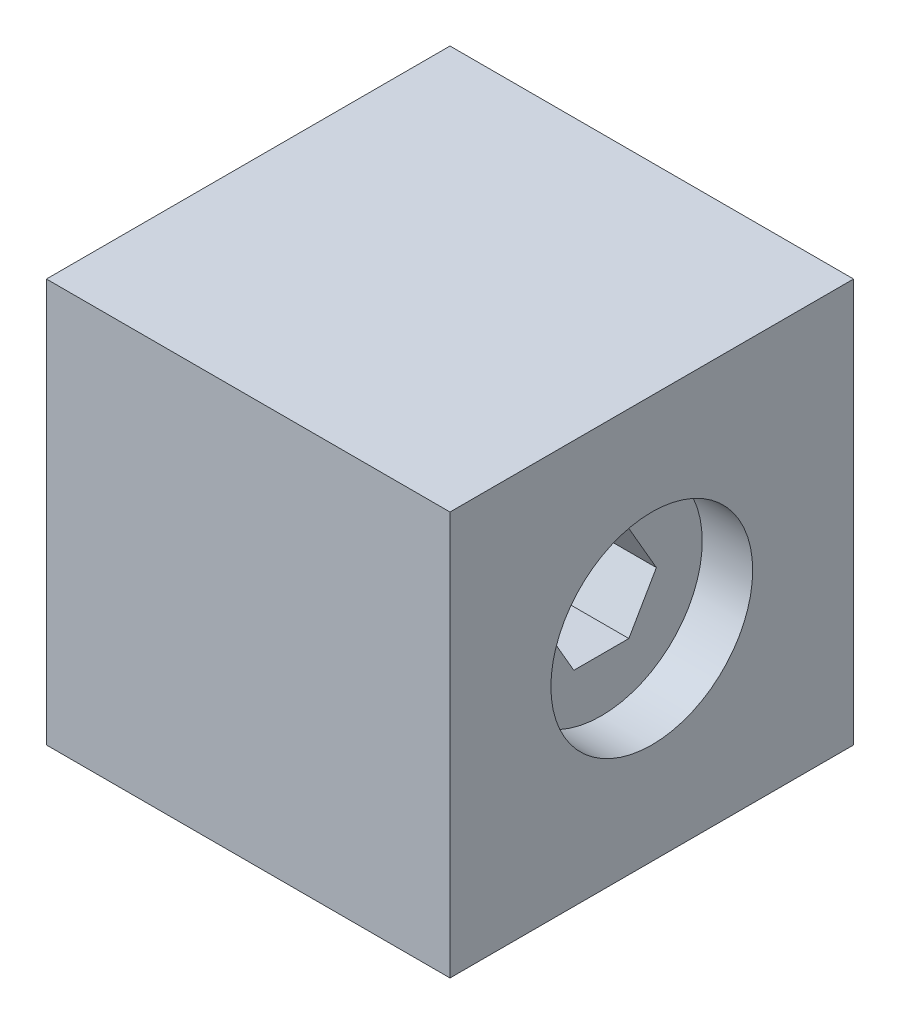
SolidWorks part; units mm, degrees
ref_plane "Front Plane" through (0, 0, 0) normal (0, 0, 1) x (1, 0, 0)
ref_plane "Top Plane" through (0, 0, 0) normal (0, 1, 0) x (1, 0, 0)
ref_plane "Right Plane" through (0, 0, 0) normal (1, 0, 0) x (0, 0, -1)
sketch "Sketch2" plane through (0, 0, 0) normal (0, 1, 0) x (1, 0, 0)
  line L1 (-25.4, -25.4) -> (25.4, -25.4)
  line L2 (-25.4, -25.4) -> (-25.4, 25.4)
  line L3 (-25.4, 25.4) -> (25.4, 25.4)
  line L4 (25.4, -25.4) -> (25.4, 25.4)
  line L5 (-25.4, -25.4) -> (25.4, 25.4) construction
  line L6 (-25.4, 25.4) -> (25.4, -25.4) construction
  point P0 (0, 0)
  dimension "D1" = 50.8
  dimension "D2" = 50.8
extrude "Boss-Extrude1" add sketch "Sketch2" along normal blind 50.8
sketch "Sketch3" plane through (0, 0, 0) normal (0, -1, 0) x (1, 0, 0)
  line L1 (-11.176, 11.176) -> (11.176, 11.176)
  line L2 (-11.176, 11.176) -> (-11.176, -11.176)
  line L3 (-11.176, -11.176) -> (11.176, -11.176)
  line L4 (11.176, 11.176) -> (11.176, -11.176)
  line L5 (-11.176, 11.176) -> (11.176, -11.176) construction
  line L6 (-11.176, -11.176) -> (11.176, 11.176) construction
  line L7 (-12.7, 12.7) -> (12.7, 12.7)
  line L8 (-12.7, 12.7) -> (-12.7, -12.7)
  line L9 (-12.7, -12.7) -> (12.7, -12.7)
  line L10 (12.7, 12.7) -> (12.7, -12.7)
  line L11 (-12.7, 12.7) -> (12.7, -12.7) construction
  line L12 (-12.7, -12.7) -> (12.7, 12.7) construction
  point P0 (0, 0)
  point P6 (0, 0)
  dimension "D1" = 22.352
  dimension "D2" = 22.352
  dimension "D3" = 25.4
  dimension "D4" = 25.4
extrude "Cut-Extrude1" cut sketch "Sketch3" against normal blind 15.24
sketch "Sketch4" plane through (25.4, 0, 0) normal (1, 0, 0) x (0, 0, -1)
  line L1 (6.9282, 25.4) -> (3.4641, 31.4)
  line L2 (3.4641, 31.4) -> (-3.4641, 31.4)
  line L3 (-3.4641, 31.4) -> (-6.9282, 25.4)
  line L4 (-6.9282, 25.4) -> (-3.4641, 19.4)
  line L5 (-3.4641, 19.4) -> (3.4641, 19.4)
  line L6 (3.4641, 19.4) -> (6.9282, 25.4)
  line L7 (-25.4, 50.8) -> (25.4, 50.8) construction
  line L8 (25.4, 50.8) -> (25.4, 0) construction
  circle A0 centre (0, 25.4) radius 6 construction
  dimension "D1" = 12
  dimension "D2" = 25.4
  dimension "D3" = 25.4
extrude "Cut-Extrude2" cut sketch "Sketch4" against normal through all
sketch "Sketch5" plane through (25.4, 0, 0) normal (1, 0, 0) x (0, 0, -1)
  line L1 (-25.4, 50.8) -> (-25.4, 0) construction
  line L2 (-25.4, 50.8) -> (25.4, 50.8) construction
  circle A0 centre (0, 25.4) radius 12.7
  dimension "D1" = 25.4
  dimension "D2" = 25.4
  dimension "D3" = 25.4
extrude "Cut-Extrude3" cut sketch "Sketch5" against normal blind 6.35
